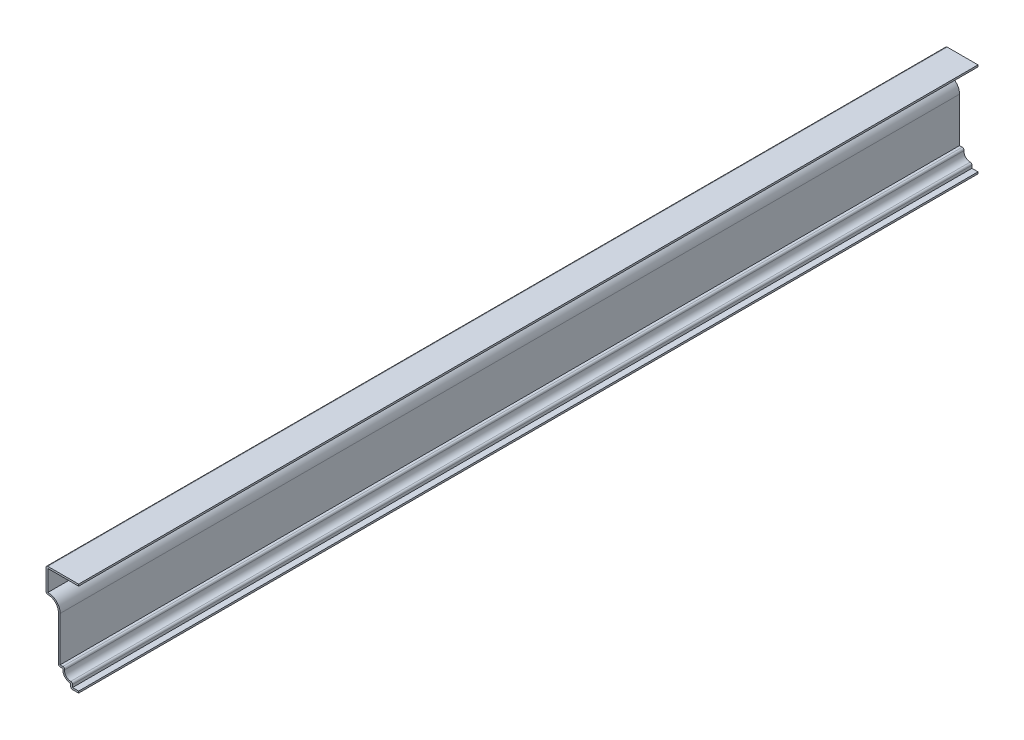
SolidWorks part; units mm, degrees
ref_plane "Front Plane" through (0, 0, 0) normal (0, 0, 1) x (1, 0, 0)
ref_plane "Top Plane" through (0, 0, 0) normal (0, 1, 0) x (1, 0, 0)
ref_plane "Right Plane" through (0, 0, 0) normal (1, 0, 0) x (0, 0, -1)
sketch "Sketch1" plane through (0, 0, 0) normal (0, 0, 1) x (1, 0, 0)
  line L0 (0, 0) -> (-5.5562, 0)
  line L1 (-5.5562, 0) -> (-5.5562, 3.175)
  line L2 (-11.1125, 9.525) -> (-14.2875, 9.525)
  line L3 (-14.2875, 9.525) -> (-14.2875, 42.2474)
  line L4 (-23.0187, 49.2125) -> (-23.0187, 66.675)
  line L5 (-23.0187, 66.675) -> (0, 66.675)
  line L6 (0, 0) -> (0, 66.675) construction
  arc A0 (-5.5562, 3.175) -> (-11.1125, 9.525) centre (-5.5562, 8.7809) cw
  arc A1 (-14.2875, 42.2474) -> (-23.0187, 49.2125) centre (-21.4312, 42.2474) ccw
  point P10 (0, 0)
  point P13 (0, 0)
  point P14 (-21.4312, 41.7688)
  dimension "D8" = 7.1437
  dimension "D1" = 5.5562
  dimension "D2" = 5.5562
  dimension "D3" = 3.175
  dimension "D4" = 8.7312
  dimension "D5" = 3.175
  dimension "D6" = 6.35
  dimension "D7" = 66.675
  dimension "D9" = 17.4625
  dimension "D10" = 39.6875
extrude "Extrude-Thin1" add sketch "Sketch1" against normal blind 635 thin
fillet "Fillet1" radius 1.27 6 edges at (-23.0187, 66.675, -317.5) (-23.0187, 49.2125, -317.5) (-14.2875, 9.525, -317.5) (-9.3959, 10.795, -317.5) (-5.5562, 0, -317.5) (-4.2862, 4.6352, -317.5)
